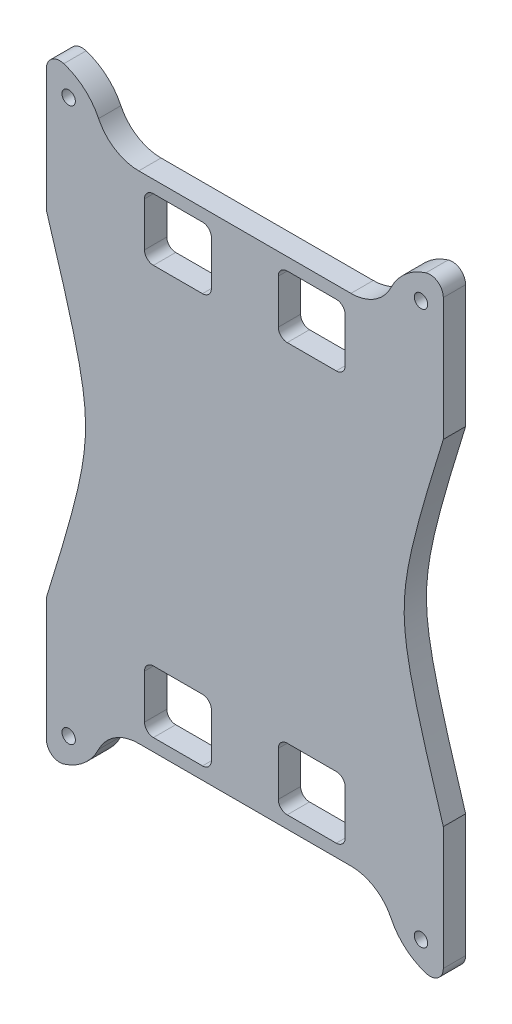
SolidWorks part; units mm, degrees
material "Acrílico (médio-alto impacto)"
ref_plane "Plano frontal" through (0, 0, 0) normal (0, 0, 1) x (1, 0, 0)
ref_plane "Plano superior" through (0, 0, 0) normal (0, 1, 0) x (1, 0, 0)
ref_plane "Plano direito" through (0, 0, 0) normal (1, 0, 0) x (0, 0, -1)
sketch "Esboço1" plane through (0, 0, 0) normal (0, 0, 1) x (1, 0, 0)
  line L0 (-8.0639, -17.8011) -> (-8.0639, -38.9203) construction
  line L1 (-31.8516, -17.8011) -> (-27.0639, -17.8011)
  line L2 (36.4361, 0.1989) -> (36.4361, -17.8011)
  line L3 (15.7238, -17.8011) -> (10.9361, -17.8011)
  line L4 (36.4361, -27.3405) -> (36.4361, -17.8011)
  line L5 (-52.5639, -27.3405) -> (-52.5639, -17.8011)
  line L6 (-52.5639, 0.1989) -> (-52.5639, -17.8011)
  line L7 (10.9361, -17.8011) -> (-27.0639, -17.8011) construction
  line L10 (36.4361, 37.7989) -> (10.9361, 37.7989) construction
  line L11 (10.9361, 93.3989) -> (-27.0639, 93.3989) construction
  line L12 (-8.0639, 93.3989) -> (-8.0639, 114.5181) construction
  line L13 (10.9361, 93.3989) -> (-27.0639, 93.3989)
  line L14 (-52.5639, 75.3989) -> (-52.5639, 93.3989)
  line L15 (-52.5639, 102.9383) -> (-52.5639, 93.3989)
  line L16 (36.4361, 102.9383) -> (36.4361, 93.3989)
  line L17 (10.9361, -17.8011) -> (-27.0639, -17.8011)
  line L18 (15.7238, 93.3989) -> (10.9361, 93.3989)
  line L19 (36.4361, 75.3989) -> (36.4361, 93.3989)
  line L20 (-31.8516, 93.3989) -> (-27.0639, 93.3989)
  arc A0 (24.7292, -23.4533) -> (32.5361, -30.2023) centre (36.4361, -17.8011) ccw
  arc A1 (24.7292, -23.4533) -> (15.7238, -17.8011) centre (15.7238, -27.8011) ccw
  arc A2 (-52.5639, -27.3405) -> (-48.6639, -30.2023) centre (-49.5639, -27.3405) ccw
  arc A3 (-40.8569, -23.4533) -> (-31.8516, -17.8011) centre (-31.8516, -27.8011) cw
  arc A4 (-40.8569, -23.4533) -> (-48.6639, -30.2023) centre (-52.5639, -17.8011) cw
  arc A5 (36.4361, -27.3405) -> (32.5361, -30.2023) centre (33.4361, -27.3405) cw
  arc A6 (36.4361, 102.9383) -> (32.5361, 105.8001) centre (33.4361, 102.9383) ccw
  arc A7 (-40.8569, 99.0511) -> (-48.6639, 105.8001) centre (-52.5639, 93.3989) ccw
  arc A8 (-40.8569, 99.0511) -> (-31.8516, 93.3989) centre (-31.8516, 103.3989) ccw
  arc A9 (-52.5639, 102.9383) -> (-48.6639, 105.8001) centre (-49.5639, 102.9383) cw
  arc A10 (24.7292, 99.0511) -> (15.7238, 93.3989) centre (15.7238, 103.3989) cw
  arc A11 (24.7292, 99.0511) -> (32.5361, 105.8001) centre (36.4361, 93.3989) cw
  conic Q0 (36.4361, 75.3989) -> (36.4361, 0.1989) control (24.7292, 37.7989) rho 0.75
  conic Q1 (-52.5639, 75.3989) -> (-52.5639, 0.1989) control (-40.8569, 37.7989) rho 0.75
  point P14 (-52.5639, -30.8011)
  point P21 (36.4361, -30.8011)
  point P45 (36.4361, 106.3989)
  point P46 (-52.5639, 106.3989)
  dimension "D1" = 26
  dimension "D2" = 20
  dimension "D8" = 13
  dimension "D9" = 3
  dimension "D11" = 10
  dimension "D3" = 25.5
  dimension "D4" = 18
  dimension "D6" = 75.2
  dimension "D10" = 9.5394
extrude "Ressalto-extrusão3" add sketch "Esboço1" along normal blind 5
sketch "Esboço3" plane through (0, 0, 0) normal (0, 0, -1) x (-1, 0, 0)
  line L1 (-4.4361, 89.2989) -> (20.5639, 89.2989)
  line L2 (-9.4361, 84.2989) -> (-9.4361, -8.7011)
  line L3 (-4.4361, -13.7011) -> (20.5639, -13.7011)
  line L4 (25.5639, 84.2989) -> (25.5639, -8.7011)
  line L5 (31.8516, -17.8011) -> (-15.7238, -17.8011) construction
  line L6 (-15.7238, 93.3989) -> (31.8516, 93.3989) construction
  line L7 (-36.4361, 75.3989) -> (-36.4361, 102.9383) construction
  line L10 (52.5639, 102.9383) -> (52.5639, 75.3989) construction
  arc A0 (20.5639, -13.7011) -> (25.5639, -8.7011) centre (20.5639, -8.7011) ccw
  arc A1 (-9.4361, -8.7011) -> (-4.4361, -13.7011) centre (-4.4361, -8.7011) ccw
  arc A2 (20.5639, 89.2989) -> (25.5639, 84.2989) centre (20.5639, 84.2989) cw
  arc A3 (-4.4361, 89.2989) -> (-9.4361, 84.2989) centre (-4.4361, 84.2989) ccw
  point P14 (-36.4361, 89.1686)
  point P17 (-9.4361, -13.7011)
  point P20 (25.5639, 89.2989)
  point P23 (-9.4361, 89.2989)
  dimension "D7" = 5
  dimension "D1" = 27
  dimension "D2" = 103
  dimension "D3" = 4.1
  dimension "D4" = 4.1
  dimension "D5" = 27
extrude "Corte-extrusão2" [suppressed] cut sketch "Esboço3" against normal blind 5
sketch "Esboço4" plane through (0, 0, 0) normal (0, 0, -1) x (-1, 0, 0)
  line L0 (-36.4361, 75.3989) -> (-36.4361, 102.9383) construction
  line L1 (52.5639, 102.9383) -> (52.5639, 75.3989) construction
  line L2 (-15.7238, 93.3989) -> (31.8516, 93.3989) construction
  line L3 (-44.641, 37.7989) -> (77.6477, 37.7989) construction
  line L4 (-12.4361, 90.5989) -> (-1.4361, 90.5989)
  line L5 (-14.4361, 88.5989) -> (-14.4361, 78.6989)
  line L6 (-12.4361, 76.6989) -> (-1.4361, 76.6989)
  line L7 (0.5639, 88.5989) -> (0.5639, 78.6989)
  line L8 (17.5639, 90.5989) -> (28.5639, 90.5989)
  line L9 (15.5639, 88.5989) -> (15.5639, 78.6989)
  line L10 (17.5639, 76.6989) -> (28.5639, 76.6989)
  line L11 (30.5639, 88.5989) -> (30.5639, 78.6989)
  line L12 (-36.4361, -27.3405) -> (-36.4361, 0.1989) construction
  line L14 (31.8516, -17.8011) -> (-15.7238, -17.8011) construction
  line L15 (30.5639, -13.0011) -> (30.5639, -3.1011)
  line L16 (17.5639, -1.1011) -> (28.5639, -1.1011)
  line L17 (15.5639, -13.0011) -> (15.5639, -3.1011)
  line L18 (17.5639, -15.0011) -> (28.5639, -15.0011)
  line L19 (0.5639, -13.0011) -> (0.5639, -3.1011)
  line L20 (-12.4361, -1.1011) -> (-1.4361, -1.1011)
  line L21 (-14.4361, -13.0011) -> (-14.4361, -3.1011)
  line L22 (-12.4361, -15.0011) -> (-1.4361, -15.0011)
  circle A0 centre (-31.4361, 99.8001) radius 1.5
  circle A1 centre (47.5639, 99.8001) radius 1.5
  arc A3 (28.5639, 76.6989) -> (30.5639, 78.6989) centre (28.5639, 78.6989) ccw
  arc A4 (28.5639, 90.5989) -> (30.5639, 88.5989) centre (28.5639, 88.5989) cw
  arc A5 (17.5639, 90.5989) -> (15.5639, 88.5989) centre (17.5639, 88.5989) ccw
  arc A6 (15.5639, 78.6989) -> (17.5639, 76.6989) centre (17.5639, 78.6989) ccw
  arc A7 (-1.4361, 76.6989) -> (0.5639, 78.6989) centre (-1.4361, 78.6989) ccw
  arc A8 (-1.4361, 90.5989) -> (0.5639, 88.5989) centre (-1.4361, 88.5989) cw
  arc A9 (-12.4361, 90.5989) -> (-14.4361, 88.5989) centre (-12.4361, 88.5989) ccw
  arc A10 (-14.4361, 78.6989) -> (-12.4361, 76.6989) centre (-12.4361, 78.6989) ccw
  arc A11 (-14.4361, -3.1011) -> (-12.4361, -1.1011) centre (-12.4361, -3.1011) cw
  arc A12 (-12.4361, -15.0011) -> (-14.4361, -13.0011) centre (-12.4361, -13.0011) cw
  arc A13 (-1.4361, -15.0011) -> (0.5639, -13.0011) centre (-1.4361, -13.0011) ccw
  arc A14 (-1.4361, -1.1011) -> (0.5639, -3.1011) centre (-1.4361, -3.1011) cw
  arc A15 (15.5639, -3.1011) -> (17.5639, -1.1011) centre (17.5639, -3.1011) cw
  arc A16 (17.5639, -15.0011) -> (15.5639, -13.0011) centre (17.5639, -13.0011) cw
  arc A17 (28.5639, -15.0011) -> (30.5639, -13.0011) centre (28.5639, -13.0011) ccw
  arc A18 (28.5639, -1.1011) -> (30.5639, -3.1011) centre (28.5639, -3.1011) cw
  circle A20 centre (47.5639, -24.2023) radius 1.5
  circle A21 centre (-31.4361, -24.2023) radius 1.5
  point P24 (30.5639, 76.6989)
  point P31 (15.5639, 76.6989)
  point P34 (0.5639, 76.6989)
  point P41 (-14.4361, 76.6989)
  point P46 (16.5034, 37.7989)
  point P79 (-14.4361, -1.1011)
  point P80 (0.5639, -1.1011)
  point P81 (15.5639, -1.1011)
  point P82 (30.5639, -1.1011)
  dimension "D1" = 3
  dimension "D3" = 3
  dimension "D4" = 5
  dimension "D5" = 6
  dimension "D6" = 5
  dimension "D7" = 6
  dimension "D16" = 2
  dimension "D10" = 52
  dimension "D11" = 52
  dimension "D12" = 2.8
  dimension "D13" = 2.8
  dimension "D14" = 15
  dimension "D15" = 15
  dimension "D17" = 90
  dimension "D18" = 55.6
extrude "Corte-extrusão3" cut sketch "Esboço4" against normal blind 10
